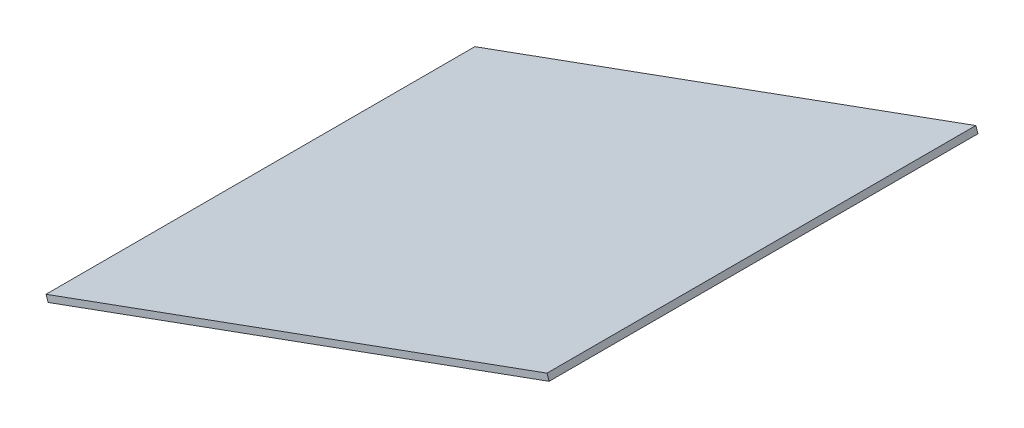
SolidWorks part; units mm, degrees
ref_plane "Front Plane" through (0, 0, 0) normal (0, 0, 1) x (1, 0, 0)
ref_plane "Top Plane" through (0, 0, 0) normal (0, 1, 0) x (1, 0, 0)
ref_plane "Right Plane" through (0, 0, 0) normal (1, 0, 0) x (0, 0, -1)
sketch "Sketch2" plane through (0, 0, 2) normal (0, 0, 1) x (1, 0, 0)
  line L1 (9976.9117, 719.2187) -> (9964.4877, 714.7007) construction
  line L10 (9742.3408, 633.9153) -> (9976.9117, 719.2187)
  line L12 (9742.3408, 633.9153) -> (9743.3661, 631.096)
  line L13 (9976.9117, 719.2187) -> (9977.937, 716.3994)
  line L15 (9743.3661, 631.096) -> (9977.937, 716.3994)
  line L17 (10010.4042, 627.1196) -> (9976.9117, 719.2187) construction
  line L18 (9742.3408, 633.9153) -> (9775.8334, 541.8162) construction
  dimension "D1" = 3
extrude "Boss-Extrude1" add sketch "Sketch2" along normal up to surface (200.8 mm away)
